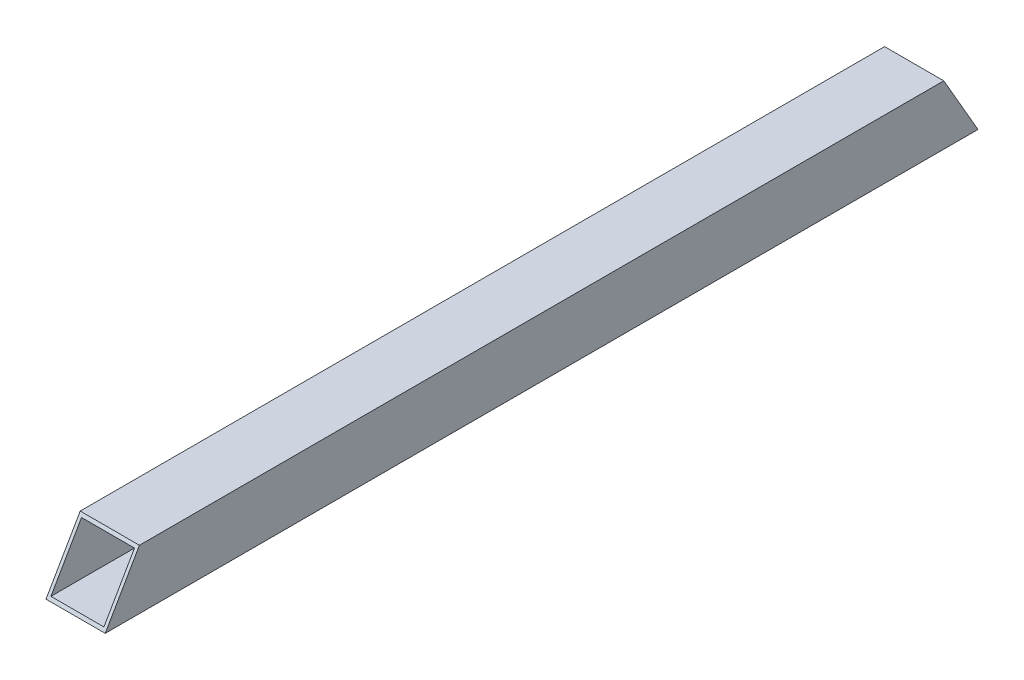
SolidWorks part; units mm, degrees
material "6061 Alloy"
ref_plane "Front Plane" through (0, 0, 0) normal (0, 0, 1) x (1, 0, 0)
ref_plane "Top Plane" through (0, 0, 0) normal (0, 1, 0) x (1, 0, 0)
ref_plane "Right Plane" through (0, 0, 0) normal (1, 0, 0) x (0, 0, -1)
sketch "Sketch1" plane through (0, 0, 0) normal (0, 0, 1) x (1, 0, 0)
  line L0 (-8.5, 8.5) -> (8.5, 8.5)
  line L1 (-9.5, -9.5) -> (9.5, -9.5)
  line L2 (-9.5, -9.5) -> (-9.5, 9.5)
  line L3 (-9.5, 9.5) -> (9.5, 9.5)
  line L4 (9.5, -9.5) -> (9.5, 9.5)
  line L5 (-9.5, -9.5) -> (9.5, 9.5) construction
  line L6 (-9.5, 9.5) -> (9.5, -9.5) construction
  line L7 (8.5, -8.5) -> (8.5, 8.5)
  line L8 (-8.5, -8.5) -> (8.5, -8.5)
  line L9 (-8.5, -8.5) -> (-8.5, 8.5)
  point P0 (0, 0)
  dimension "D1" = 19
  dimension "D2" = 19
  dimension "D3" = 1
extrude "Boss-Extrude1" add sketch "Sketch1" along normal blind 280
sketch "Sketch4" plane through (9.5, 0, 0) normal (1, 0, 0) x (0, 0, -1)
  line L0 (-280, -9.5) -> (-269.0303, 9.5)
  line L1 (-280, 9.5) -> (0, 9.5) construction
extrude "Cut-Extrude3" cut sketch "Sketch4" against normal through all and the other way through all
sketch "Sketch5" plane through (9.5, 0, 0) normal (1, 0, 0) x (0, 0, -1)
  line L0 (0, -9.5) -> (-10.9697, 9.5)
  line L1 (-269.0303, 9.5) -> (0, 9.5) construction
extrude "Cut-Extrude4" cut sketch "Sketch5" against normal through all and the other way through all flip side to cut
